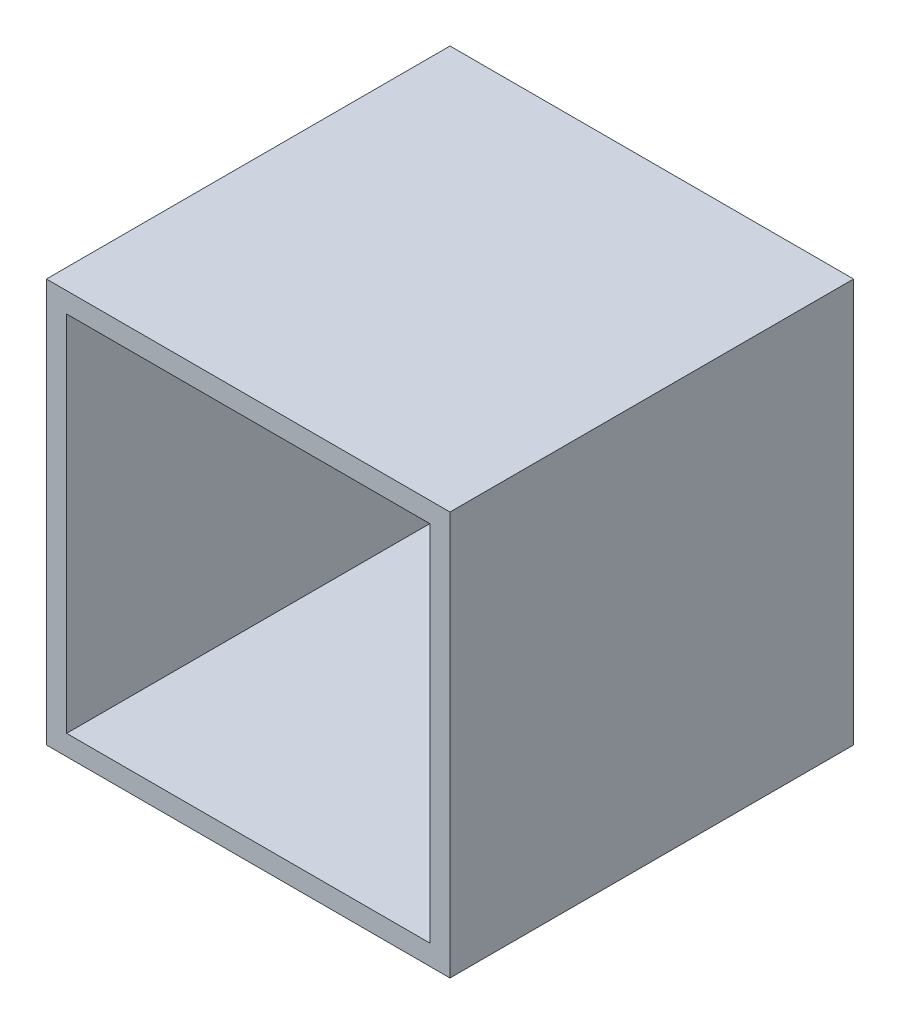
SolidWorks part; units mm, degrees
ref_plane "Front Plane" through (0, 0, 0) normal (0, 0, 1) x (1, 0, 0)
ref_plane "Top Plane" through (0, 0, 0) normal (0, 1, 0) x (1, 0, 0)
ref_plane "Right Plane" through (0, 0, 0) normal (1, 0, 0) x (0, 0, -1)
sketch "Sketch1" plane through (0, 0, 0) normal (0, 0, 1) x (1, 0, 0)
  line L1 (-55.8985, 13.704) -> (44.1015, 13.704)
  line L2 (-55.8985, 13.704) -> (-55.8985, -86.296)
  line L3 (-55.8985, -86.296) -> (44.1015, -86.296)
  line L4 (44.1015, 13.704) -> (44.1015, -86.296)
  dimension "D1" = 100
  dimension "D2" = 100
extrude "Boss-Extrude1" add sketch "Sketch1" along normal blind 100
shell "Shell1" thickness 5
